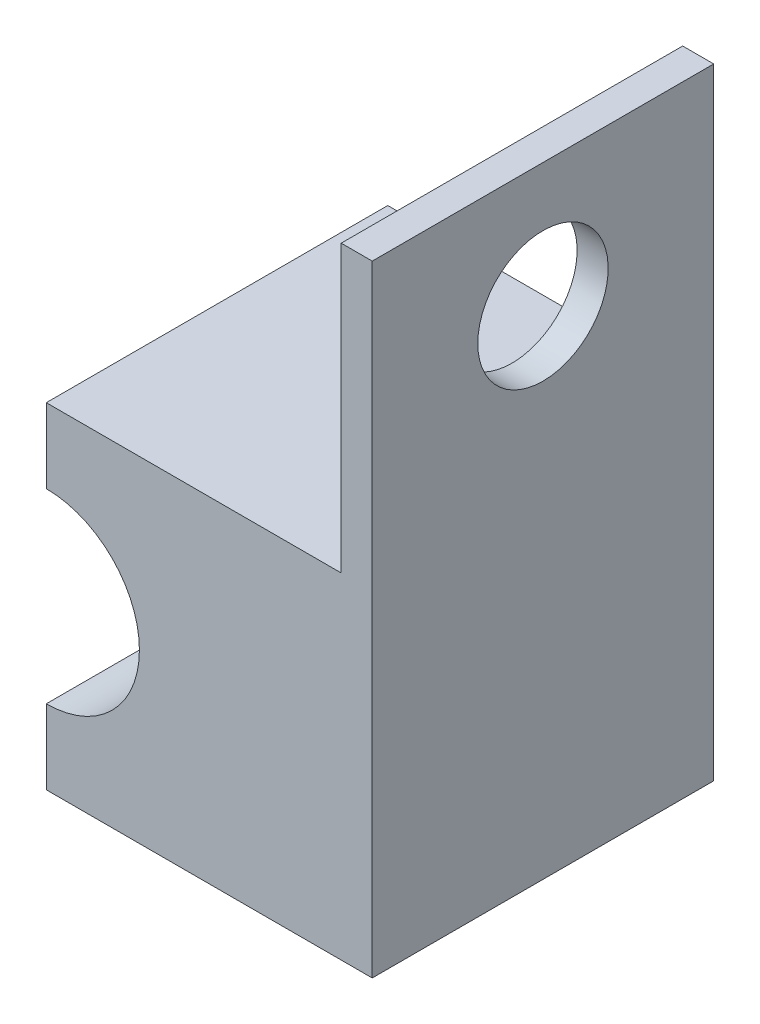
SolidWorks part; units mm, degrees
material "ABS PC"
ref_plane "Front Plane" through (0, 0, 0) normal (0, 0, 1) x (1, 0, 0)
ref_plane "Top Plane" through (0, 0, 0) normal (0, 1, 0) x (1, 0, 0)
ref_plane "Right Plane" through (0, 0, 0) normal (1, 0, 0) x (0, 0, -1)
sketch "Sketch1" plane through (0, 0, 0) normal (0, 0, 1) x (1, 0, 0)
  line L0 (0, 0) -> (0, 2.4)
  line L2 (0, 8.4) -> (0, 10.8)
  line L3 (0, 10.8) -> (10.5, 10.8)
  line L4 (10.5, 10.8) -> (10.5, 0)
  line L5 (10.5, 0) -> (0, 0)
  arc A0 (0, 2.4) -> (0, 8.4) centre (0, 5.4) ccw
  dimension "D3" = 2.4
  dimension "D1" = 2.4
  dimension "D2" = 6
  dimension "D4" = 10.5
extrude "Boss-Extrude1" add sketch "Sketch1" along normal blind 11
sketch "Sketch2" plane through (0, 10.8, 0) normal (0, 1, 0) x (1, 0, 0)
  line L0 (10.5, 0) -> (9.5, 0)
  line L1 (10.5, 0) -> (0, 0) construction
  line L2 (9.5, 0) -> (9.5, -11)
  line L3 (10.5, -11) -> (0, -11) construction
  line L4 (9.5, -11) -> (10.5, -11)
  line L5 (10.5, -11) -> (10.5, 0)
  dimension "D1" = 1
extrude "Boss-Extrude2" add sketch "Sketch2" along normal blind 9.2
sketch "Sketch3" plane through (9.5, 0, 0) normal (-1, 0, 0) x (0, 0, 1)
  line L0 (5.5, 10.8) -> (5.5, 16)
  line L1 (0, 10.8) -> (11, 10.8) construction
  circle A0 centre (5.5, 16) radius 2.1
  dimension "D2" = 4.2
  dimension "D1" = 5.2
extrude "Cut-Extrude1" cut sketch "Sketch3" against normal blind 10
